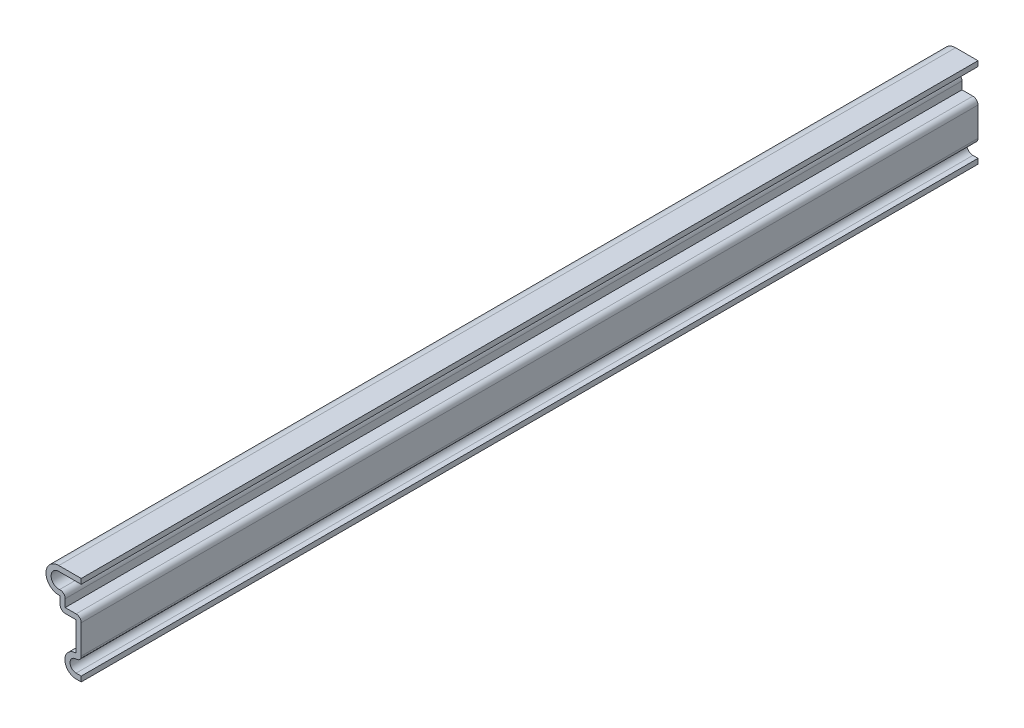
SolidWorks part; units mm, degrees
ref_plane "Front Plane" through (0, 0, 0) normal (0, 0, 1) x (1, 0, 0)
ref_plane "Top Plane" through (0, 0, 0) normal (0, 1, 0) x (1, 0, 0)
ref_plane "Right Plane" through (0, 0, 0) normal (1, 0, 0) x (0, 0, -1)
sketch "Sketch1" plane through (0, 0, 0) normal (0, 0, 1) x (1, 0, 0)
  line L0 (0, 22.225) -> (-5.5562, 22.225)
  line L1 (-5.2388, 15.8909) -> (-5.2388, 12.7159)
  line L2 (-5.2388, 12.7159) -> (-1.27, 12.7159)
  line L3 (-1.27, 12.7159) -> (-1.27, 5.5562)
  line L4 (-1.27, 0) -> (0, 0)
  arc A0 (-5.5562, 22.225) -> (-5.2388, 15.8909) centre (-5.5562, 19.05) ccw
  arc A1 (-1.27, 5.5562) -> (-1.27, 0) centre (-1.27, 2.7781) ccw
  point P8 (0, 0)
  point P10 (-6.2702, 19.05)
  dimension "D2" = 3.175
  dimension "D6" = 2.7781
  dimension "D8" = 8.7312
  dimension "D3" = 3.175
  dimension "D4" = 22.225
  dimension "D5" = 3.9688
  dimension "D7" = 1.27
extrude "Extrude-Thin2" add sketch "Sketch1" against normal blind 222.25 thin thin type one direction reverse wall 1.27
fillet "Fillet1" radius 1.27 4 edges at (0, 3.5915, -111.125) (0, 13.9859, -111.125) (-3.9688, 17.997, -111.125) (-5.2388, 12.7159, -111.125)
